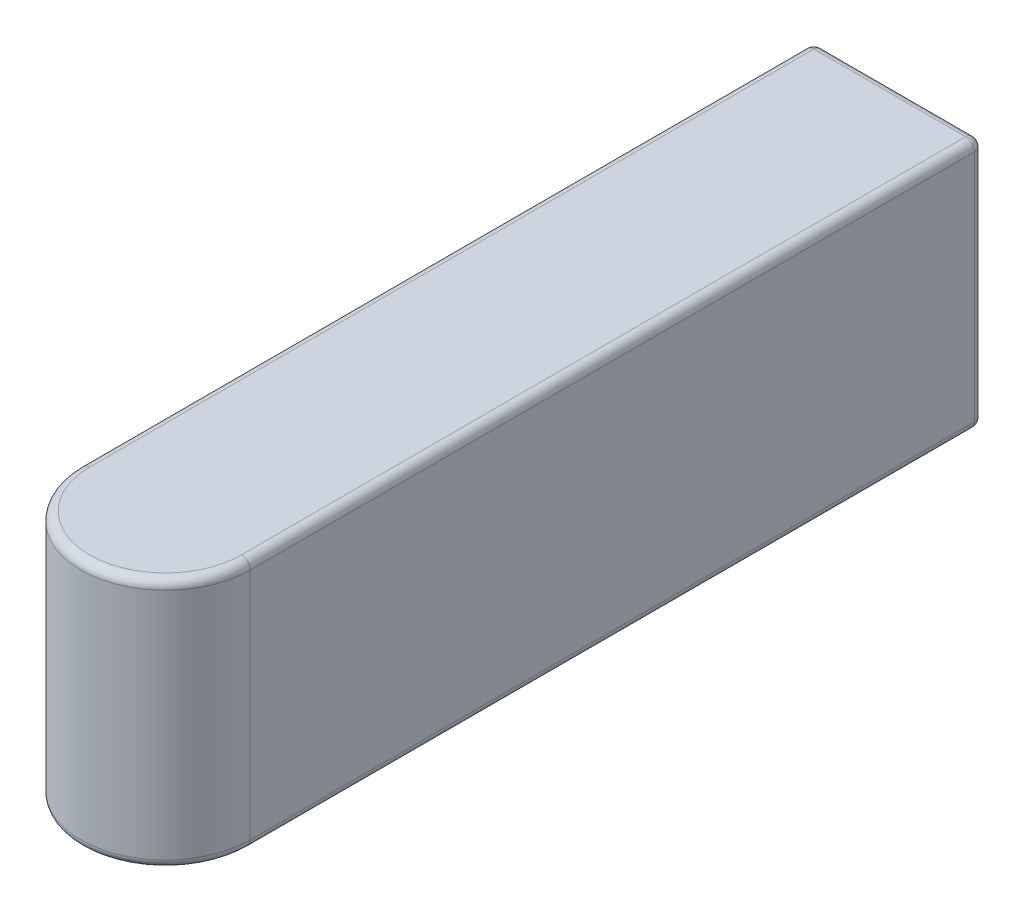
SolidWorks part; units mm, degrees
ref_plane "Front Plane" through (0, 0, 0) normal (0, 0, 1) x (1, 0, 0)
ref_plane "Top Plane" through (0, 0, 0) normal (0, 1, 0) x (1, 0, 0)
ref_plane "Right Plane" through (0, 0, 0) normal (1, 0, 0) x (0, 0, -1)
sketch "Sketch1" plane through (0, 0, 0) normal (0, 1, 0) x (1, 0, 0)
  line L1 (0, 0) -> (29, 0)
  line L2 (0, 0) -> (0, -125.5)
  line L3 (0, -125.5) -> (29, -125.5)
  line L4 (29, 0) -> (29, -125.5)
  arc A0 (0, -125.5) -> (29, -125.5) centre (14.5, -125.5) ccw
  point P6 (14.5, -140)
  dimension "D1" = 29
  dimension "D2" = 140
extrude "Boss-Extrude1" add sketch "Sketch1" along normal blind 43 contours L4 L1 L2 L3 | L3 A0
fillet "Fillet1" radius 1.5 10 edges at (0, 43, 62.75) (29, 43, 62.75) (14.5, 43, 140) (0, 0, 62.75) (29, 0, 62.75) (29, 21.5, 0) (14.5, 43, 0) (0, 21.5, 0) (14.5, 0, 0) (14.5, 0, 140)
ref_plane "Plane1" through (14.5, 0, 0) normal (1, 0, 0) x (0, 0, -1)
